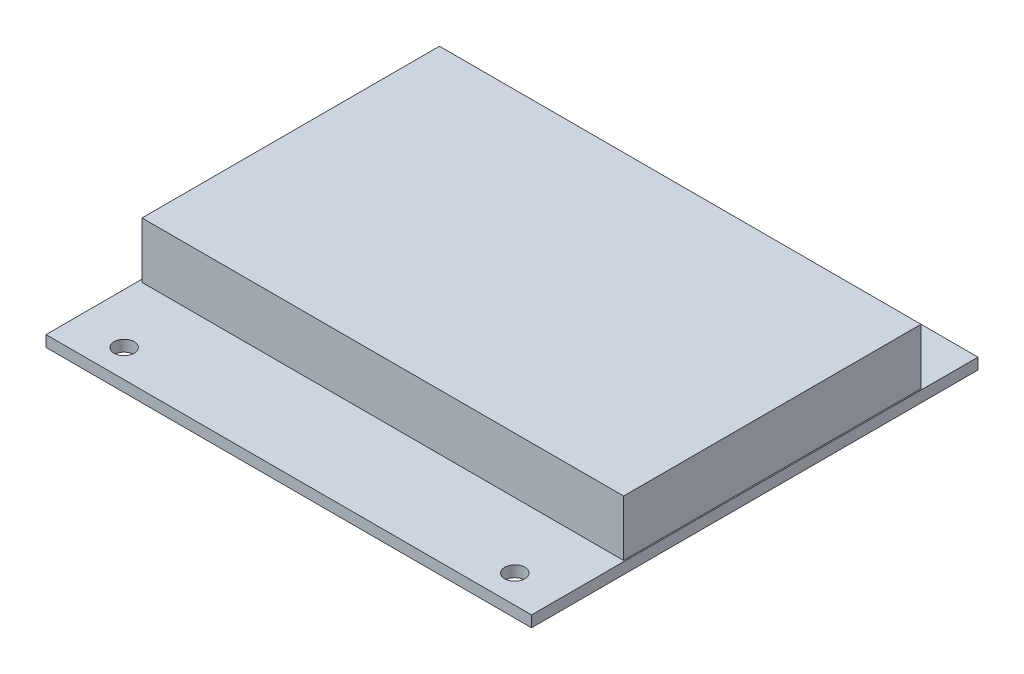
SolidWorks part; units mm, degrees
ref_plane "Front Plane" through (0, 0, 0) normal (0, 0, 1) x (1, 0, 0)
ref_plane "Top Plane" through (0, 0, 0) normal (0, 1, 0) x (1, 0, 0)
ref_plane "Right Plane" through (0, 0, 0) normal (1, 0, 0) x (0, 0, -1)
sketch "Sketch1" plane through (0, 0, 0) normal (0, 1, 0) x (1, 0, 0)
  line L1 (0, 0) -> (87, 0)
  line L2 (0, 0) -> (0, 80)
  line L3 (0, 80) -> (87, 80)
  line L4 (87, 0) -> (87, 80)
  dimension "D1" = 87
  dimension "D2" = 80
extrude "PCB" add sketch "Sketch1" along normal blind 2
sketch "Sketch2" plane through (0, 2, 0) normal (0, 1, 0) x (1, 0, 0)
  line L0 (87, 80) -> (0, 80) construction
  line L1 (0, 80) -> (0, 0) construction
  circle A0 centre (9, 75) radius 1.8
  dimension "D1" = 3.6
  dimension "D2" = 5
  dimension "D3" = 9
extrude "Attachment Holes" cut sketch "Sketch2" against normal through all
pattern_linear "LPattern1" count 2 spacing 70 along (1, 0, 0) count 2 spacing 70 along (0, 0, 1) of "Attachment Holes"
sketch "Sketch3" plane through (0, 2, 0) normal (0, 1, 0) x (1, 0, 0)
  line L2 (0, 80) -> (0, 0) construction
  line L3 (0.5, 70) -> (86.8, 70)
  line L4 (0.5, 70) -> (0.5, 16.7)
  line L6 (0.5, 16.7) -> (86.8, 16.7)
  line L9 (86.8, 70) -> (86.8, 16.7)
  line L10 (87, 80) -> (0, 80) construction
  dimension "D1" = 86.3
  dimension "D2" = 53.3
  dimension "D3" = 0.5
  dimension "D4" = 10
extrude "Iduino" add sketch "Sketch3" along normal blind 10
